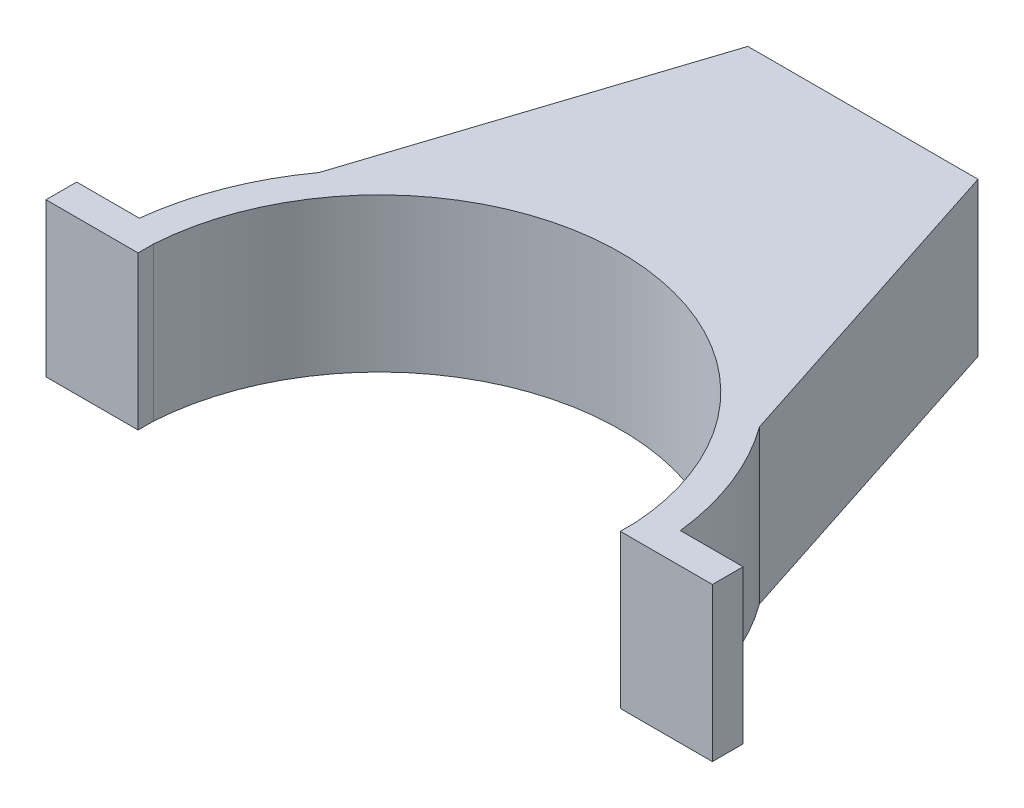
SolidWorks part; units mm, degrees
material "ABS"
ref_plane "Front Plane" through (0, 0, 0) normal (0, 0, 1) x (1, 0, 0)
ref_plane "Top Plane" through (0, 0, 0) normal (0, 1, 0) x (1, 0, 0)
ref_plane "Right Plane" through (0, 0, 0) normal (1, 0, 0) x (0, 0, -1)
sketch "Sketch1" plane through (0, 0, 0) normal (0, 1, 0) x (1, 0, 0)
  circle A0 centre (0, 0) radius 39.9923
  circle A1 centre (0, 0) radius 45.0723
  dimension "D1" = 79.9846
  dimension "D2" = 5.08
extrude "Boss-Extrude1" add sketch "Sketch1" along normal blind 25.4
ref_plane "Plane1" through (0, 12.7, 0) normal (0, 1, 0) x (1, 0, 0)
sketch "Sketch2" plane through (0, 12.7, 0) normal (0, 1, 0) x (1, 0, 0)
  line L0 (45.0723, 0) -> (19.05, 80.0853)
  line L1 (19.05, 80.0853) -> (-19.05, 80.0853)
  line L2 (-19.05, 80.0853) -> (-45.0723, 0)
  line L3 (42.6566, -0.7849) -> (17.2046, 77.5453)
  line L4 (17.2046, 77.5453) -> (-17.2046, 77.5453)
  line L5 (-17.2046, 77.5453) -> (-42.6566, -0.7849)
  line L6 (42.6566, -0.7849) -> (45.0723, 0)
  line L7 (-45.0723, 0) -> (-42.6566, -0.7849)
  circle A0 centre (0, 0) radius 45.0723 construction
  point P4 (0, 80.0853)
  dimension "D1" = 38.1
  dimension "D2" = 2.54
extrude "Boss-Extrude2" add sketch "Sketch2" along normal mid plane 25.4
sketch "Sketch3" plane through (0, 25.4, 0) normal (0, 1, 0) x (1, 0, 0)
  line L0 (-17.2046, 77.5453) -> (17.2046, 77.5453) construction
  line L1 (-32.1308, 31.6089) -> (-17.2046, 77.5453) construction
  line L2 (17.2046, 77.5453) -> (32.1308, 31.6089) construction
  line L3 (-17.2046, 77.5453) -> (17.2046, 77.5453)
  line L4 (-32.1308, 31.6089) -> (-17.2046, 77.5453)
  line L5 (17.2046, 77.5453) -> (32.1308, 31.6089)
  arc A0 (32.1308, 31.6089) -> (-32.1308, 31.6089) centre (0, 0) ccw construction
  arc A1 (32.1308, 31.6089) -> (-32.1308, 31.6089) centre (0, 0) ccw
extrude "Boss-Extrude3" add sketch "Sketch3" against normal blind 12.7
sketch "Sketch4" plane through (0, 0, 0) normal (0, 0, 1) x (1, 0, 0)
  line L1 (-45.0723, 0) -> (45.0723, 0)
  line L2 (-45.0723, 0) -> (-45.0723, 25.4)
  line L3 (-45.0723, 25.4) -> (45.0723, 25.4)
  line L4 (45.0723, 0) -> (45.0723, 25.4)
extrude "Cut-Extrude1" cut sketch "Sketch4" against normal blind 2.54 and the other way through all
sketch "Sketch5" plane through (0, 0, -2.54) normal (0, 0, 1) x (1, 0, 0)
  line L0 (0, 0) -> (0, 38.7969) construction
  line L1 (-45.0007, 25.4) -> (-39.9116, 25.4)
  line L3 (-45.0865, 0) -> (-39.9116, 0)
  line L4 (-39.9116, 25.4) -> (-39.9116, 0)
  line L9 (-45.0007, 25.4) -> (-55.1607, 25.4)
  line L10 (-55.1607, 25.4) -> (-55.1607, 0)
  line L11 (-55.1607, 0) -> (-45.0865, 0)
  line L12 (55.1607, 25.4) -> (55.1607, 0)
  line L13 (45.0007, 25.4) -> (55.1607, 25.4)
  line L14 (45.0007, 25.4) -> (39.9116, 25.4)
  line L15 (39.9116, 25.4) -> (39.9116, 0)
  line L16 (45.0865, 0) -> (39.9116, 0)
  line L17 (55.1607, 0) -> (45.0865, 0)
  dimension "D1" = 10.16
extrude "Boss-Extrude4" add sketch "Sketch5" along normal mid plane 5.08
